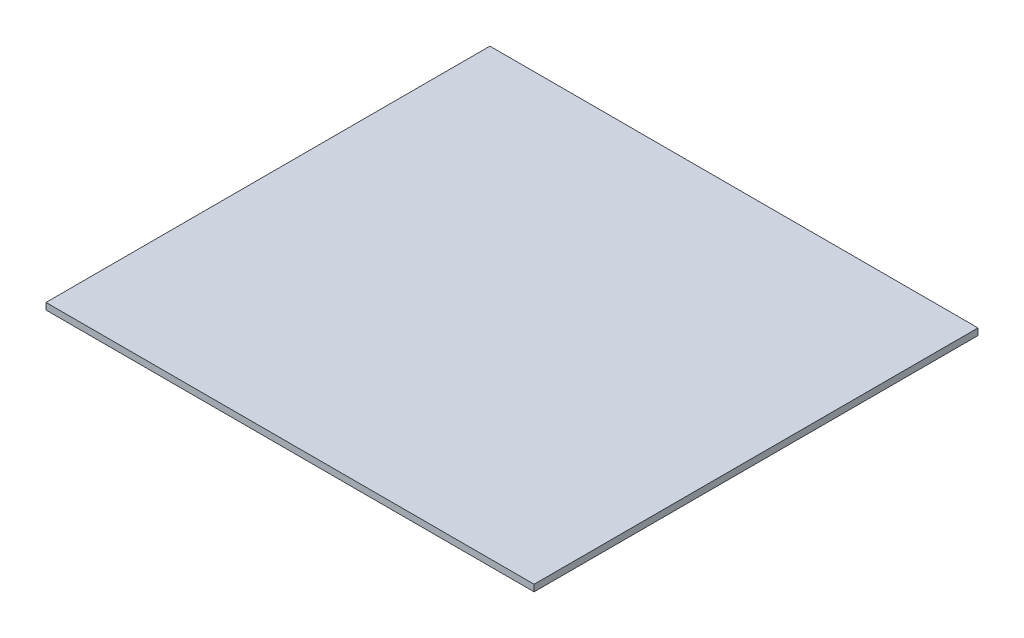
SolidWorks part; units mm, degrees
material "6061 Alloy"
ref_plane "Front Plane" through (0, 0, 0) normal (0, 0, 1) x (1, 0, 0)
ref_plane "Top Plane" through (0, 0, 0) normal (0, 1, 0) x (1, 0, 0)
ref_plane "Right Plane" through (0, 0, 0) normal (1, 0, 0) x (0, 0, -1)
sketch "Sketch1" plane through (0, 0, 0) normal (0, 1, 0) x (1, 0, 0)
  line L1 (-110.5, -100.5) -> (110.5, -100.5)
  line L2 (-110.5, -100.5) -> (-110.5, 100.5)
  line L3 (-110.5, 100.5) -> (110.5, 100.5)
  line L4 (110.5, -100.5) -> (110.5, 100.5)
  line L5 (-110.5, -100.5) -> (110.5, 100.5) construction
  line L6 (-110.5, 100.5) -> (110.5, -100.5) construction
  point P0 (0, 0)
  dimension "D1" = 221
  dimension "D2" = 201
extrude "Boss-Extrude1" add sketch "Sketch1" along normal blind 3
